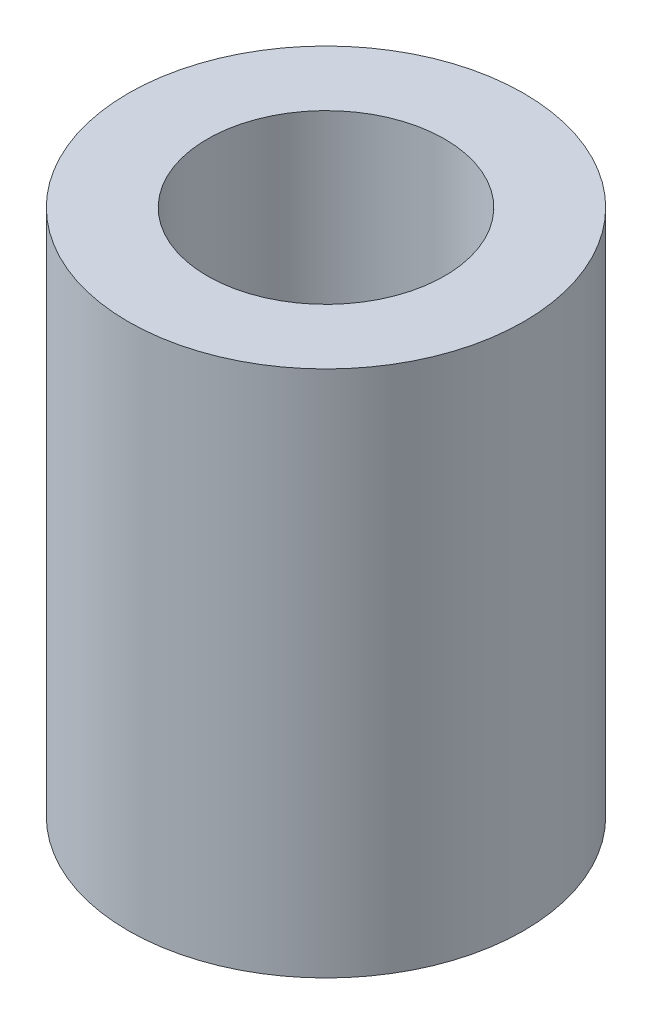
SolidWorks part; units mm, degrees
ref_plane "Front Plane" through (0, 0, 0) normal (0, 0, 1) x (1, 0, 0)
ref_plane "Top Plane" through (0, 0, 0) normal (0, 1, 0) x (1, 0, 0)
ref_plane "Right Plane" through (0, 0, 0) normal (1, 0, 0) x (0, 0, -1)
sketch "Sketch1" plane through (0, 0, 0) normal (0, 1, 0) x (1, 0, 0)
  circle A0 centre (0, 0) radius 2.25
  circle A1 centre (0, 0) radius 1.35
  dimension "D1" = 2.7
  dimension "D2" = 4.5
extrude "Boss-Extrude1" add sketch "Sketch1" along normal blind 6
